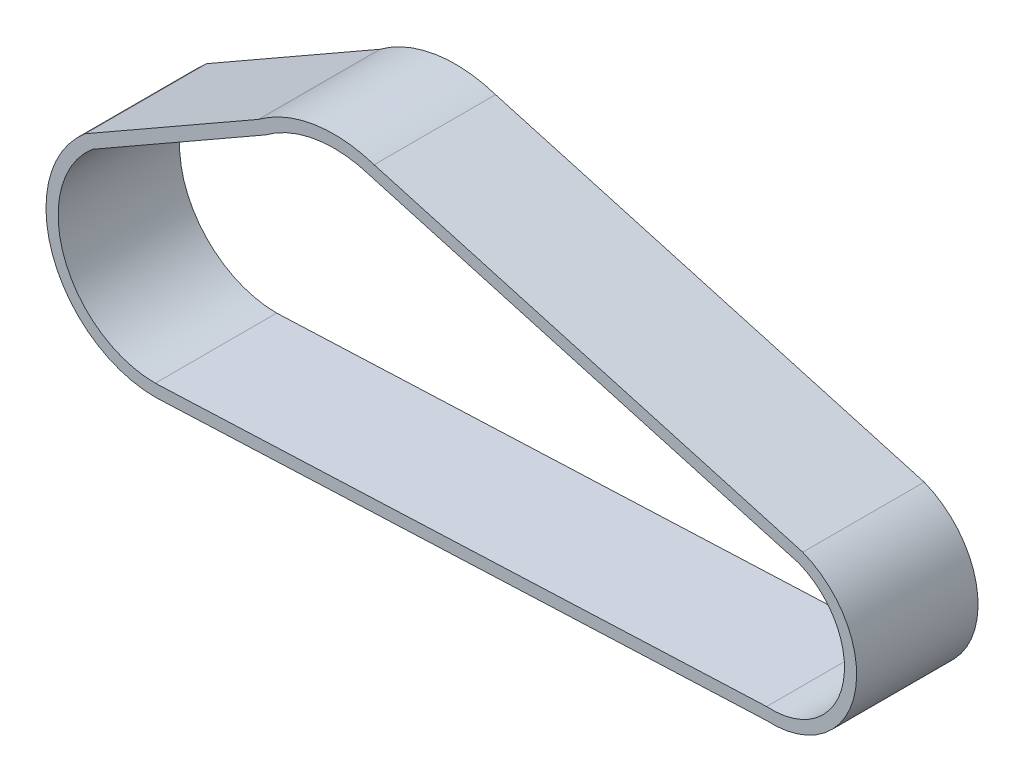
SolidWorks part; units mm, degrees
material "POLIURETANICHE (11671)"
ref_plane "Front Plane" through (0, 0, 0) normal (0, 0, 1) x (1, 0, 0)
ref_plane "Top Plane" through (0, 0, 0) normal (0, 1, 0) x (1, 0, 0)
ref_plane "Right Plane" through (0, 0, 0) normal (1, 0, 0) x (0, 0, -1)
sketch "Schizzo2" plane through (-3.6262, -4.3882, 0) normal (0, 0, 1) x (1, 0, 0)
  line L0 (0, 0) -> (0.777, 0) construction
  line L1 (0, 0) -> (0, 0.777) construction
  line L2 (38.3162, 24.49) -> (-138.0506, 74.3611)
  line L3 (-181.4524, 67.3388) -> (-252.6864, 26.6076)
  line L4 (-226.734, -43.8305) -> (25.0444, -33.2649)
  arc A0 (25.0444, -33.2649) -> (38.3162, 24.49) centre (27.1029, -3.3356) ccw
  arc A1 (-138.0506, 74.3611) -> (-181.4524, 67.3388) centre (-153.0561, 29.4682) ccw
  arc A2 (-252.6864, 26.6076) -> (-226.734, -43.8305) centre (-226.734, -3.8305) ccw
  point P12 (0, 0)
  point P13 (0, 0)
  point P14 (-128.8062, 89.5467)
  point P15 (-171.6837, 84.6034)
  point P16 (-138.456, 84.6034)
  point P17 (-145.5544, 75.1418)
  point P18 (-181.4524, 67.3388)
  point P19 (-138.0506, 74.3611)
  point P20 (0, 0)
  dimension "D2" = 30
extrude "Estrusione-Sottile1" add sketch "Schizzo2" along normal blind 25 and the other way blind 25 thin
ref_plane "Piano2" through (0, 0, -14) normal (0, 0, -1) x (-1, 0, 0)
ref_plane "Piano3" through (0, 0, 14) normal (0, 0, 1) x (1, 0, 0)
scale "Scale2" scale about centroid uniform scaling yes scale factor 0.93
